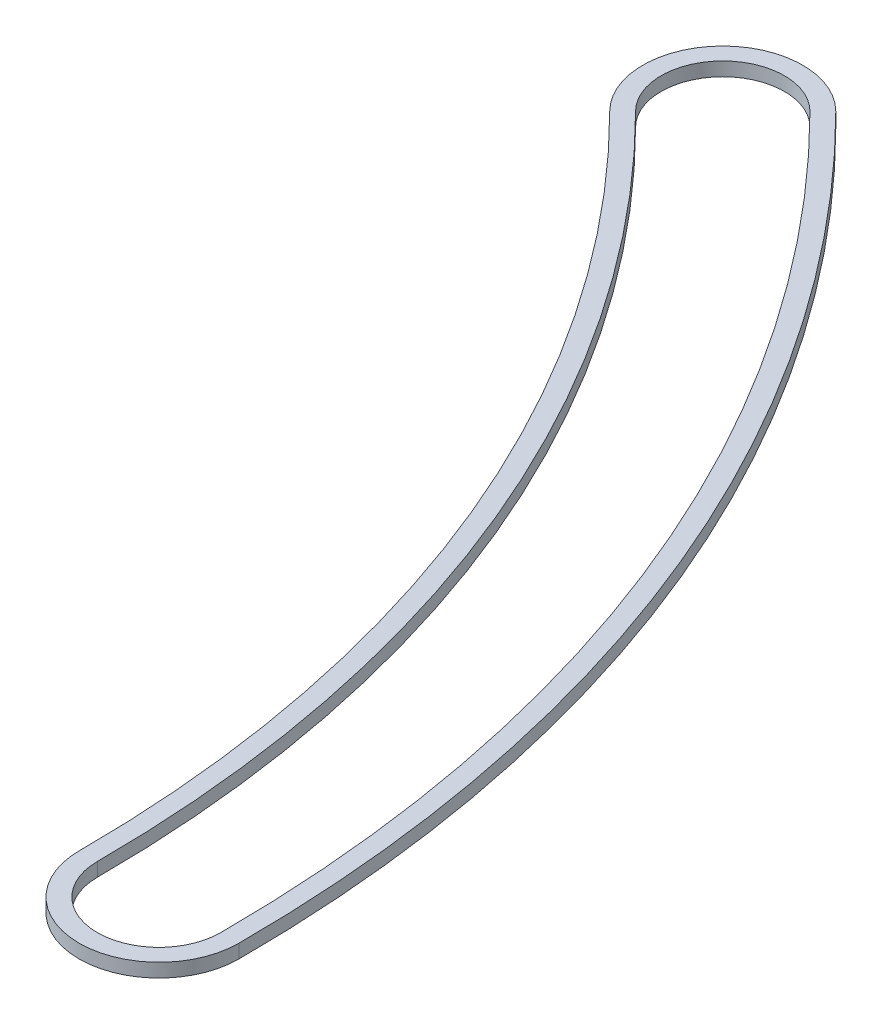
SolidWorks part; units mm, degrees
material "NBR"
ref_plane "Front Plane" through (0, 0, 0) normal (0, 0, 1) x (1, 0, 0)
ref_plane "Top Plane" through (0, 0, 0) normal (0, 1, 0) x (1, 0, 0)
ref_plane "Right Plane" through (0, 0, 0) normal (1, 0, 0) x (0, 0, -1)
sketch "Sketch1" plane through (0, 0, 0) normal (0, 1, 0) x (1, 0, 0)
  line L0 (0, 0) -> (53.5223, 53.5223) construction
  line L1 (0, 0) -> (75.692, 0) construction
  arc A0 (75.692, 0) -> (53.5223, 53.5223) centre (0, 0) ccw construction
  arc A1 (80.137, 0) -> (56.6654, 56.6654) centre (0, 0) ccw
  arc A2 (71.247, 0) -> (50.3792, 50.3792) centre (0, 0) ccw
  arc A3 (71.247, 0) -> (80.137, 0) centre (75.692, 0) ccw
  arc A4 (56.6654, 56.6654) -> (50.3792, 50.3792) centre (53.5223, 53.5223) ccw
  arc A5 (75.692, 0) -> (53.5223, 53.5223) centre (0, 0) ccw construction
  arc A6 (79.121, 0) -> (55.947, 55.947) centre (0, 0) ccw
  arc A7 (72.263, 0) -> (51.0977, 51.0977) centre (0, 0) ccw
  arc A8 (72.263, 0) -> (79.121, 0) centre (75.692, 0) ccw
  arc A9 (55.947, 55.947) -> (51.0977, 51.0977) centre (53.5223, 53.5223) ccw
  point P4 (69.9303, 28.9661)
  point P13 (69.9303, 28.9661)
  dimension "D4" = 75.692
  dimension "D3" = 4.445
  dimension "D1" = 45
  dimension "D2" = 1.016
extrude "Boss-Extrude1" add sketch "Sketch1" along normal blind 0.762
equation "\"w\"= 0.04"
equation "\"D2@Sketch1\"=\"w\""
equation "\"D3@Sketch1\" = .185 - .01'10 thou smaller than channel rad"
